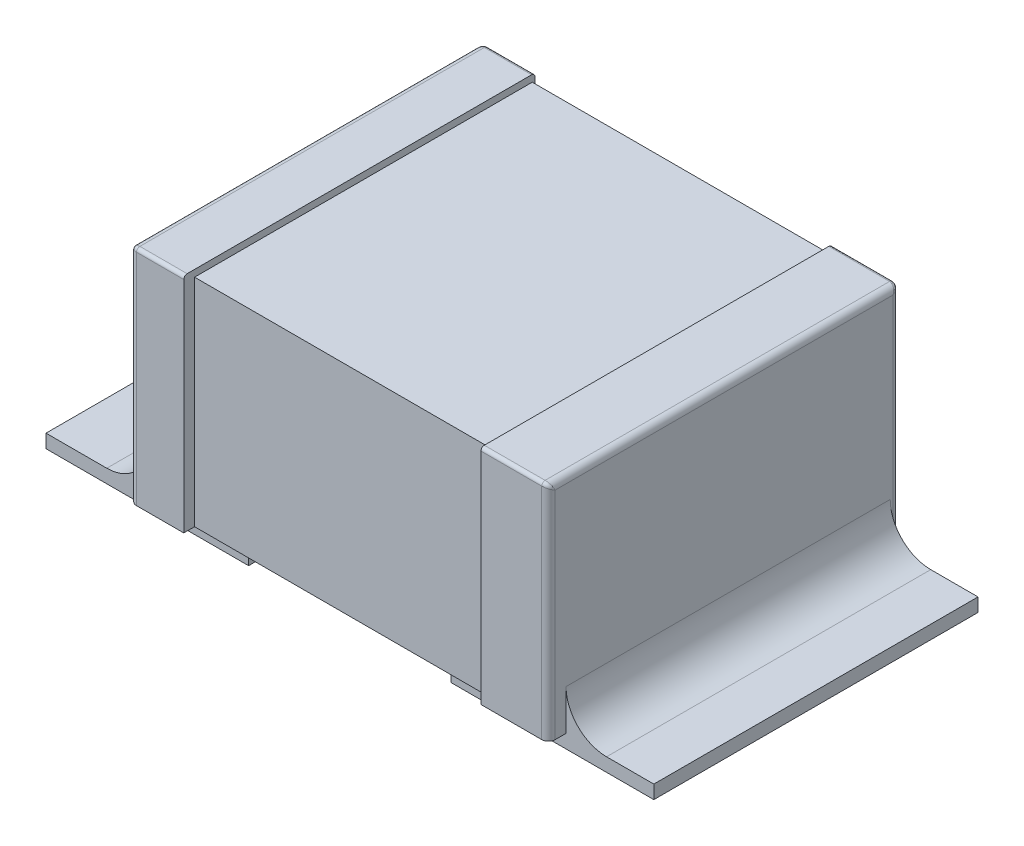
SolidWorks part; units mm, degrees
material "6063-O"
ref_plane "Front Plane" through (0, 0, 0) normal (0, 0, 1) x (1, 0, 0)
ref_plane "Top Plane" through (0, 0, 0) normal (0, 1, 0) x (1, 0, 0)
ref_plane "Right Plane" through (0, 0, 0) normal (1, 0, 0) x (0, 0, -1)
sketch "Sketch1" plane through (0, 0, 0) normal (1, 0, 0) x (0, 0, -1)
  line L0 (1.43, 0) -> (-1.43, 0) construction
  line L1 (-1.25, 0.1) -> (1.25, 0.1)
  line L2 (-1.25, 0.1) -> (-1.25, 1.7)
  line L3 (-1.25, 1.7) -> (1.25, 1.7)
  line L4 (1.25, 0.1) -> (1.25, 1.7)
  line L5 (0, 0.9625) -> (0, -0.9625) construction
  dimension "D1" = 2.5
  dimension "D2" = 1.6
  dimension "D3" = 0.1
  dimension "D4" = 1.25
extrude "Boss-Extrude1" add sketch "Sketch1" along normal mid plane 2.2
sketch "Sketch3" plane through (1.1, 0, 0) normal (1, 0, 0) x (0, 0, -1)
  line L0 (0, 0.9625) -> (0, -0.9625) construction
  line L1 (-1.305, 1.75) -> (1.245, 1.75)
  line L2 (-1.33, 1.725) -> (-1.33, 0.1)
  line L3 (-1.33, 0.1) -> (1.27, 0.1)
  line L4 (1.27, 1.725) -> (1.27, 0.1)
  line L6 (1.43, 0) -> (-1.43, 0) construction
  arc A2 (1.245, 1.75) -> (1.27, 1.725) centre (1.245, 1.725) cw
  arc A3 (-1.305, 1.75) -> (-1.33, 1.725) centre (-1.305, 1.725) ccw
  point P15 (1.27, 1.75)
  point P18 (-1.33, 1.75)
  dimension "D5" = 0.025
  dimension "D1" = 2.6
  dimension "D2" = 1.27
  dimension "D3" = 1.65
  dimension "D4" = 0.1
extrude "Boss-Extrude2" add sketch "Sketch3" along normal blind 0.5
sketch "Sketch5" plane through (-1.1, 0, 0) normal (-1, 0, 0) x (0, 0, 1)
  line L0 (1.305, 1.75) -> (-1.245, 1.75) construction
  line L1 (-1.245, 1.75) -> (1.305, 1.75)
  line L2 (-1.27, 1.725) -> (-1.27, 0.1)
  line L3 (-1.27, 0.1) -> (1.33, 0.1)
  line L4 (1.33, 1.725) -> (1.33, 0.1)
  line L5 (1.33, 1.725) -> (1.33, 0.1) construction
  line L6 (1.33, 0.1) -> (-1.27, 0.1) construction
  line L7 (-1.27, 1.725) -> (-1.27, 0.1) construction
  arc A2 (1.305, 1.75) -> (1.33, 1.725) centre (1.305, 1.725) cw
  arc A3 (-1.245, 1.75) -> (-1.27, 1.725) centre (-1.245, 1.725) ccw
  dimension "D1" = 0.025
extrude "Boss-Extrude3" add sketch "Sketch5" along normal blind 0.4
sketch "Sketch6" plane through (0, 0, 0) normal (0, 1, 0) x (1, 0, 0)
  line L0 (0, -0.9075) -> (0, 0.9075) construction
  line L1 (-2.25, 1.2) -> (-0.75, 1.2)
  line L2 (-2.25, 1.2) -> (-2.25, -1.2)
  line L3 (-2.25, -1.2) -> (-0.75, -1.2)
  line L4 (-0.75, 1.2) -> (-0.75, -1.2)
  line L5 (-0.9075, 0) -> (0.9075, 0) construction
  line L7 (0.75, 1.2) -> (2.25, 1.2)
  line L8 (0.75, 1.2) -> (0.75, -1.2)
  line L9 (0.75, -1.2) -> (2.25, -1.2)
  line L10 (2.25, 1.2) -> (2.25, -1.2)
  dimension "D1" = 1.5
  dimension "D2" = 2.4
  dimension "D3" = 0.75
  dimension "D4" = 1.2
  dimension "D5" = 0.75
extrude "Boss-Extrude4" add sketch "Sketch6" along normal blind 0.1
fillet "Fillet3" radius 0.05 10 edges at (1.6, 0.9125, 1.33) (1.6, 1.7427, 1.3227) (1.6, 1.75, 0.03) (1.6, 1.7427, -1.2627) (-1.5, 0.9125, 1.33) (-1.5, 1.7427, 1.3227) (-1.5, 1.75, 0.03) (-1.5, 1.7427, -1.2627) (1.6, 0.9125, -1.27) (-1.5, 0.9125, -1.27)
fillet "Fillet4" radius 0.3 2 edges at (1.6, 0.1, 0) (-1.5, 0.1, 0)
